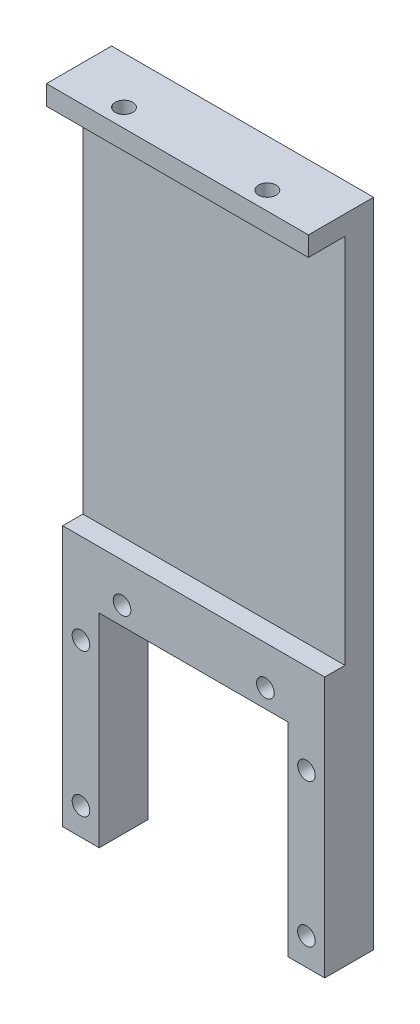
SolidWorks part; units mm, degrees
material "6061 Alloy"
ref_plane "Front Plane" through (0, 0, 0) normal (0, 0, 1) x (1, 0, 0)
ref_plane "Top Plane" through (0, 0, 0) normal (0, 1, 0) x (1, 0, 0)
ref_plane "Right Plane" through (0, 0, 0) normal (1, 0, 0) x (0, 0, -1)
sketch "Sketch1" plane through (0, 0, 0) normal (0, 0, 1) x (1, 0, 0)
  line L1 (-20.1, -50) -> (20.1, -50)
  line L2 (-20.1, -50) -> (-20.1, 50)
  line L3 (-20.1, 50) -> (20.1, 50)
  line L4 (20.1, -50) -> (20.1, 50)
  line L5 (-20.1, -50) -> (20.1, 50) construction
  line L6 (-20.1, 50) -> (20.1, -50) construction
  point P0 (0, 0)
  dimension "D1" = 40.2
  dimension "D2" = 100
extrude "Boss-Extrude1" add sketch "Sketch1" along normal blind 10
sketch "Sketch3" plane through (0, 0, 10) normal (0, 0, 1) x (1, 0, 0)
  line L0 (-20.1, -50) -> (20.1, -50) construction
  line L1 (-14.5, -18.8) -> (14.5, -18.8)
  line L2 (-14.5, -18.8) -> (-14.5, -50)
  line L3 (-14.5, -50) -> (14.5, -50)
  line L4 (14.5, -18.8) -> (14.5, -50)
  line L5 (-14.5, -18.8) -> (14.5, -50) construction
  line L6 (-14.5, -50) -> (14.5, -18.8) construction
  point P0 (0, -34.4)
  dimension "D1" = 29
  dimension "D2" = 31.2
sketch "Sketch2" plane through (0, 0, 10) normal (0, 0, 1) x (1, 0, 0)
  line L1 (17.3, -45.8) -> (-17.3, -45.8) construction
  line L2 (-11, -16) -> (11, -16) construction
  line L3 (-17.3, -16) -> (17.3, -16) construction
  line L4 (-17.3, -16) -> (-17.3, -23.8) construction
  line L5 (-20.1, -50) -> (20.1, -50) construction
  line L6 (17.3, -16) -> (17.3, -23.8) construction
  line L7 (-17.3, -16) -> (17.3, -23.8) construction
  line L8 (-17.3, -23.8) -> (17.3, -16) construction
  line L10 (17.3, -45.8) -> (17.3, -23.8) construction
  line L11 (17.3, -23.8) -> (-17.3, -23.8) construction
  line L12 (-17.3, -45.8) -> (-17.3, -23.8) construction
  line L13 (17.3, -45.8) -> (-17.3, -23.8) construction
  line L14 (17.3, -23.8) -> (-17.3, -45.8) construction
  circle A0 centre (17.3, -23.8) radius 1.35
  circle A1 centre (11, -16) radius 1.35
  circle A2 centre (-17.3, -23.8) radius 1.35
  circle A3 centre (-11, -16) radius 1.35
  circle A4 centre (-17.3, -45.8) radius 1.35
  circle A5 centre (17.3, -45.8) radius 1.35
  point P8 (0, -34.8)
  point P11 (0, -19.9)
  point P12 (0, -16)
  dimension "D1" = 22
  dimension "D2" = 2.7
  dimension "D3" = 22
  dimension "D4" = 7.8
  dimension "D5" = 34.6
  dimension "D6" = 4.2
sketch "Sketch7" plane through (0, 0, 10) normal (0, 0, 1) x (1, 0, 0)
  line L0 (20.1, -50) -> (20.1, 50) construction
  line L1 (-20.1, -50) -> (20.1, -50)
  line L2 (-20.1, -50) -> (-20.1, 46.8)
  line L3 (-20.1, 46.8) -> (20.1, 46.8)
  line L4 (20.1, -50) -> (20.1, 46.8)
  line L5 (-20.1, -50) -> (20.1, 46.8) construction
  line L6 (-20.1, 46.8) -> (20.1, -50) construction
  line L7 (-20.1, 50) -> (-20.1, -50) construction
  line L8 (20.1, 50) -> (-20.1, 50) construction
  point P0 (0, -1.6)
  dimension "D1" = 3.2
extrude "Cut-Extrude5" cut sketch "Sketch7" against normal blind 2.5
sketch "Sketch4" plane through (0, 0, 10) normal (0, 0, 1) x (1, 0, 0)
  line L0 (-20.1, 50) -> (-20.1, 46.8) construction
  line L1 (-20.1, 47) -> (20.1, 47)
  line L2 (-20.1, 47) -> (-20.1, -10)
  line L3 (-20.1, -10) -> (20.1, -10)
  line L4 (20.1, 47) -> (20.1, -10)
  line L5 (-20.1, 47) -> (20.1, -10) construction
  line L6 (-20.1, -10) -> (20.1, 47) construction
  line L7 (20.1, 50) -> (-20.1, 50) construction
  line L8 (20.1, 46.8) -> (20.1, 50) construction
  line L9 (-20.1, -50) -> (20.1, -50) construction
  point P0 (0, 18.5)
  dimension "D1" = 3
  dimension "D2" = 40
extrude "Cut-Extrude1" cut sketch "Sketch4" against normal blind 5.6
extrude "Cut-Extrude2" cut sketch "Sketch3" against normal through all
extrude "Cut-Extrude3" cut sketch "Sketch2" against normal through all
sketch "Sketch6" plane through (0, 50, 0) normal (0, 1, 0) x (-1, 0, 0)
  line L0 (11, 7.2) -> (-11, 7.2) construction
  line L2 (-20.1, 10) -> (20.1, 10) construction
  circle A0 centre (-11, 7.2) radius 1.35
  circle A1 centre (11, 7.2) radius 1.35
  point P4 (0, 7.2)
  dimension "D1" = 2.7
  dimension "D2" = 22
  dimension "D3" = 2.8
extrude "Cut-Extrude4" cut sketch "Sketch6" against normal up to next
